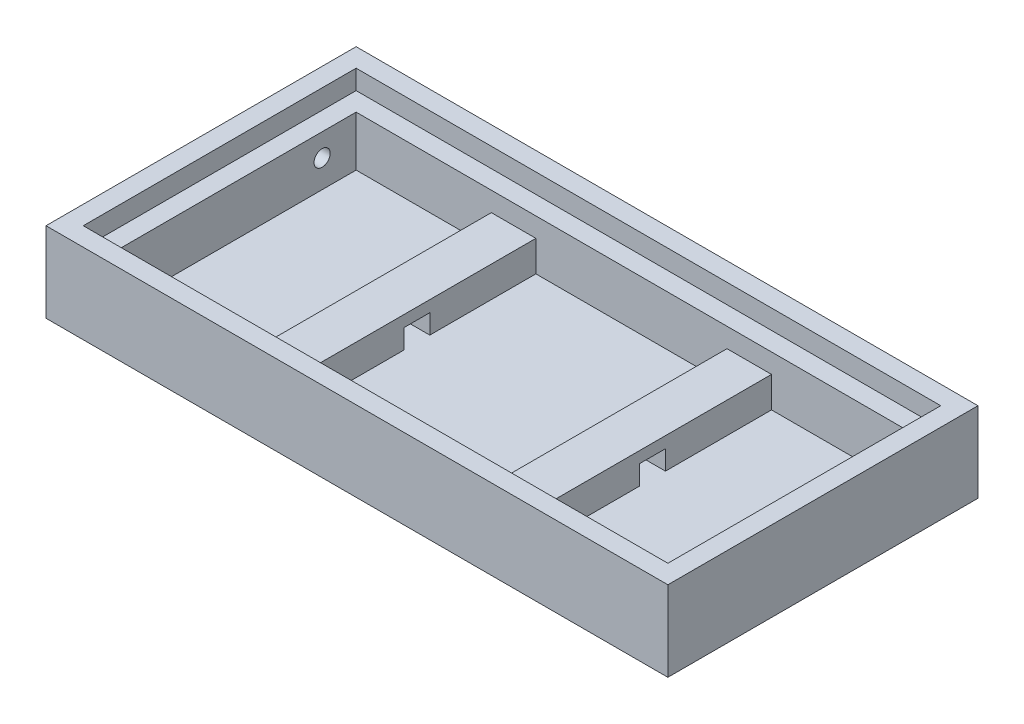
SolidWorks part; units mm, degrees
material "Plywood"
ref_plane "Front Plane" through (0, 0, 0) normal (0, 0, 1) x (1, 0, 0)
ref_plane "Top Plane" through (0, 0, 0) normal (0, 1, 0) x (1, 0, 0)
ref_plane "Right Plane" through (0, 0, 0) normal (1, 0, 0) x (0, 0, -1)
sketch "Sketch3" plane through (0, 0, 0) normal (0, 1, 0) x (1, 0, 0)
  line L1 (0, 0) -> (1219.2, 0)
  line L2 (0, 0) -> (0, 608.0125)
  line L3 (0, 608.0125) -> (1219.2, 608.0125)
  line L4 (1219.2, 0) -> (1219.2, 608.0125)
  dimension "D1" = 1219.2
  dimension "D2" = 608.0125
extrude "Boss-Extrude1" add sketch "Sketch3" along normal blind 20.6375
sketch "Sketch4" plane through (0, 20.6375, 0) normal (0, 1, 0) x (1, 0, 0)
  line L10 (0, 0) -> (1219.2, 0) construction
  line L11 (1219.2, 0) -> (1219.2, 608.0125) construction
  line L12 (1219.2, 608.0125) -> (0, 608.0125) construction
  line L13 (0, 608.0125) -> (0, 0) construction
  line L14 (1182.6875, 36.5125) -> (1182.6875, 571.5)
  line L15 (36.5125, 36.5125) -> (1182.6875, 36.5125)
  line L16 (36.5125, 571.5) -> (36.5125, 36.5125)
  line L17 (1182.6875, 571.5) -> (36.5125, 571.5)
  line L18 (1182.6875, 36.5125) -> (1182.6875, 571.5)
  line L19 (36.5125, 36.5125) -> (1182.6875, 36.5125)
  line L20 (36.5125, 571.5) -> (36.5125, 36.5125)
  line L21 (1182.6875, 571.5) -> (36.5125, 571.5)
  line L22 (0, 0) -> (1219.2, 0)
  line L23 (1219.2, 0) -> (1219.2, 608.0125)
  line L24 (1219.2, 608.0125) -> (0, 608.0125)
  line L25 (0, 608.0125) -> (0, 0)
  dimension "D1" = 36.5125
extrude "Boss-Extrude2" add sketch "Sketch4" along normal blind 136.525
sketch "Sketch5" plane through (0, 20.6375, 0) normal (0, 1, 0) x (1, 0, 0)
  line L10 (36.5125, 36.5125) -> (1182.6875, 36.5125) construction
  line L11 (1182.6875, 36.5125) -> (1182.6875, 571.5) construction
  line L12 (1182.6875, 571.5) -> (36.5125, 571.5) construction
  line L13 (36.5125, 571.5) -> (36.5125, 36.5125) construction
  line L14 (1146.175, 73.025) -> (1146.175, 534.9875)
  line L15 (73.025, 73.025) -> (1146.175, 73.025)
  line L16 (73.025, 534.9875) -> (73.025, 73.025)
  line L17 (1146.175, 534.9875) -> (73.025, 534.9875)
  line L18 (1146.175, 73.025) -> (1146.175, 534.9875)
  line L19 (73.025, 73.025) -> (1146.175, 73.025)
  line L20 (73.025, 534.9875) -> (73.025, 73.025)
  line L21 (1146.175, 534.9875) -> (73.025, 534.9875)
  line L22 (36.5125, 36.5125) -> (1182.6875, 36.5125)
  line L23 (1182.6875, 36.5125) -> (1182.6875, 571.5)
  line L24 (1182.6875, 571.5) -> (36.5125, 571.5)
  line L25 (36.5125, 571.5) -> (36.5125, 36.5125)
  dimension "D1" = 36.5125
extrude "Boss-Extrude3" add sketch "Sketch5" along normal blind 98.425
sketch "Sketch6" plane through (0, 20.6375, 0) normal (0, 1, 0) x (1, 0, 0)
  line L0 (1146.175, 534.9875) -> (73.025, 534.9875) construction
  line L1 (800.1, 534.9875) -> (887.4125, 534.9875)
  line L2 (800.1, 534.9875) -> (800.1, 73.025)
  line L3 (800.1, 73.025) -> (887.4125, 73.025)
  line L4 (887.4125, 534.9875) -> (887.4125, 73.025)
  line L5 (73.025, 73.025) -> (1146.175, 73.025) construction
  line L6 (1146.175, 73.025) -> (1146.175, 534.9875) construction
  line L7 (338.1375, 534.9875) -> (425.45, 534.9875)
  line L8 (338.1375, 534.9875) -> (338.1375, 73.025)
  line L9 (338.1375, 73.025) -> (425.45, 73.025)
  line L10 (425.45, 534.9875) -> (425.45, 73.025)
  dimension "D1" = 87.3125
  dimension "D2" = 87.3125
  dimension "D3" = 258.7625
  dimension "D4" = 549.275
extrude "Boss-Extrude4" add sketch "Sketch6" along normal blind 60.325
sketch "Sketch7" plane through (887.4125, 0, 0) normal (1, 0, 0) x (0, 0, -1)
  line L0 (73.025, 20.6375) -> (534.9875, 20.6375) construction
  line L1 (276.225, 20.6375) -> (327.025, 20.6375)
  line L2 (276.225, 20.6375) -> (276.225, 58.7375)
  line L3 (276.225, 58.7375) -> (327.025, 58.7375)
  line L4 (327.025, 20.6375) -> (327.025, 58.7375)
  line L5 (73.025, 80.9625) -> (73.025, 20.6375) construction
  dimension "D1" = 203.2
  dimension "D2" = 50.8
  dimension "D3" = 38.1
extrude "Cut-Extrude1" cut sketch "Sketch7" against normal up to surface (549.275 mm away) up to face at (338.1375, 50.8, -304.0063)
sketch "Sketch8" plane through (73.025, 0, 0) normal (1, 0, 0) x (0, 0, -1)
  line L0 (534.9875, 20.6375) -> (73.025, 20.6375) construction
  line L1 (534.9875, 119.0625) -> (534.9875, 20.6375) construction
  circle A0 centre (468.3125, 74.6125) radius 15.875
  dimension "D1" = 31.75
  dimension "D2" = 53.975
  dimension "D3" = 66.675
extrude "Cut-Extrude2" cut sketch "Sketch8" against normal up to surface (73.025 mm away) up to face at (0, 78.5813, -304.0062)
